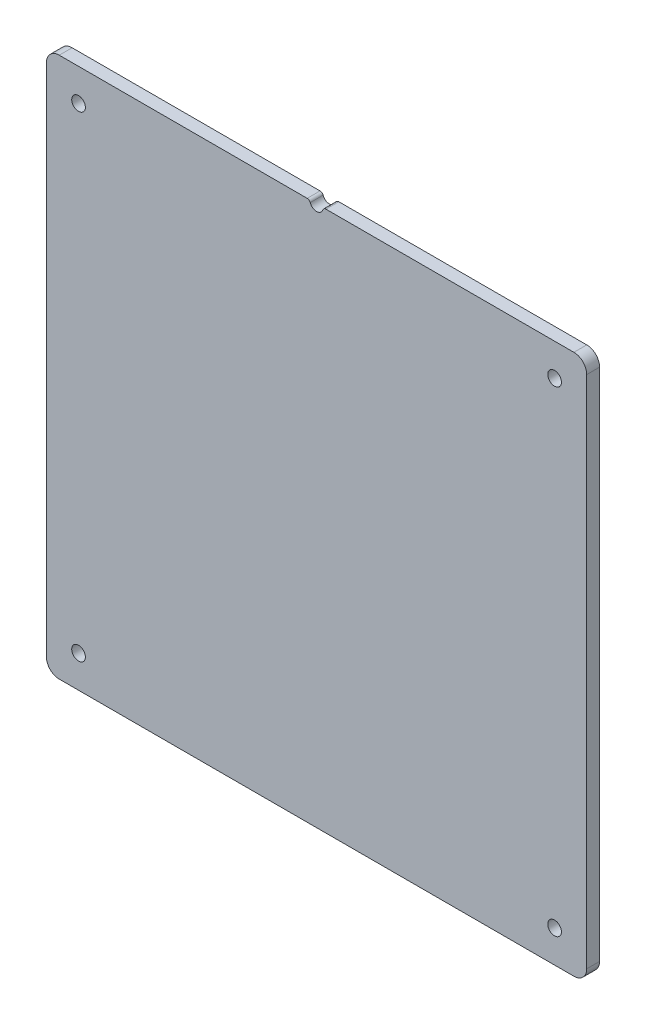
SolidWorks part; units mm, degrees
material "PC High Viscosity"
ref_plane "Front Plane" through (0, 0, 0) normal (0, 0, 1) x (1, 0, 0)
ref_plane "Top Plane" through (0, 0, 0) normal (0, 1, 0) x (1, 0, 0)
ref_plane "Right Plane" through (0, 0, 0) normal (1, 0, 0) x (0, 0, -1)
sketch "Sketch1" plane through (0, 0, 0) normal (0, 0, 1) x (1, 0, 0)
  line L1 (-133.35, -133.35) -> (133.35, -133.35)
  line L2 (-133.35, -133.35) -> (-133.35, 133.35)
  line L3 (-133.35, 133.35) -> (133.35, 133.35)
  line L4 (133.35, -133.35) -> (133.35, 133.35)
  line L5 (-133.35, -133.35) -> (133.35, 133.35) construction
  line L6 (-133.35, 133.35) -> (133.35, -133.35) construction
  point P0 (0, 0)
  dimension "D1" = 266.7
extrude "Boss-Extrude1" add sketch "Sketch1" along normal blind 6.35
hole_wizard "1/4 Clearance Hole1" positions "Sketch2" profile "Sketch3" hole size "1/4" standard "ANSI Inch" end condition through all
sketch "Sketch2" plane through (0, 0, 6.35) normal (0, 0, 1) x (1, 0, 0)
  line L0 (0, 133.35) -> (0, -133.35) construction
  line L1 (133.35, 133.35) -> (-133.35, 133.35) construction
  line L2 (-133.35, -133.35) -> (133.35, -133.35) construction
  line L3 (-133.35, 0) -> (133.35, 0) construction
  line L4 (-133.35, 133.35) -> (-133.35, -133.35) construction
  line L5 (133.35, -133.35) -> (133.35, 133.35) construction
  line L7 (-103.1875, -103.1875) -> (103.1875, -103.1875) construction
  line L8 (-103.1875, -103.1875) -> (-103.1875, 103.1875) construction
  line L9 (-103.1875, 103.1875) -> (103.1875, 103.1875) construction
  line L10 (103.1875, -103.1875) -> (103.1875, 103.1875) construction
  line L11 (-103.1875, -103.1875) -> (103.1875, 103.1875) construction
  line L12 (-103.1875, 103.1875) -> (103.1875, -103.1875) construction
  line L13 (-133.35, 104.775) -> (-117.475, 104.775) construction
  line L16 (-104.775, 117.475) -> (-104.775, 133.35) construction
  arc A0 (-117.475, 104.775) -> (-104.775, 117.475) centre (-117.475, 117.475) ccw construction
  point P0 (-117.475, 117.475)
  point P17 (-117.475, -117.475)
  point P19 (117.475, -117.475)
  point P20 (117.475, 117.475)
  point P145 (0, 0)
  dimension "D4" = 12.7
  dimension "D1" = 15.875
  dimension "D2" = 15.875
  dimension "D3" = 206.375
sketch "Sketch3" plane through (-117.475, 117.475, 6.35) normal (1, 0, 0) x (0, -1, 0)
  line L0 (0, 0) -> (0, 6.35)
  line L1 (0, 6.35) -> (3.3782, 6.35)
  line L2 (3.3782, 6.35) -> (3.3782, 0)
  line L5 (3.3782, 0) -> (0, 0)
  line L11 (0, -6.35) -> (0, 107.95) construction
  dimension "Thru Hole Dia." = 6.7564
  dimension "Thru Hole Depth" = 6.35
fillet "Fillet1" radius 6.35 4 edges at (133.35, -133.35, 3.175) (-133.35, -133.35, 3.175) (133.35, 133.35, 3.175) (-133.35, 133.35, 3.175)
sketch "Sketch4" plane through (0, 0, 6.35) normal (0, 0, 1) x (1, 0, 0)
  line L0 (127, 133.35) -> (-127, 133.35) construction
  circle A0 centre (0, 133.35) radius 3.302
  dimension "D1" = 6.604
extrude "Cut-Extrude1" cut sketch "Sketch4" against normal through all
fillet "Fillet2" radius 1.5875 2 edges at (-3.302, 133.35, 3.175) (3.302, 133.35, 3.175)
